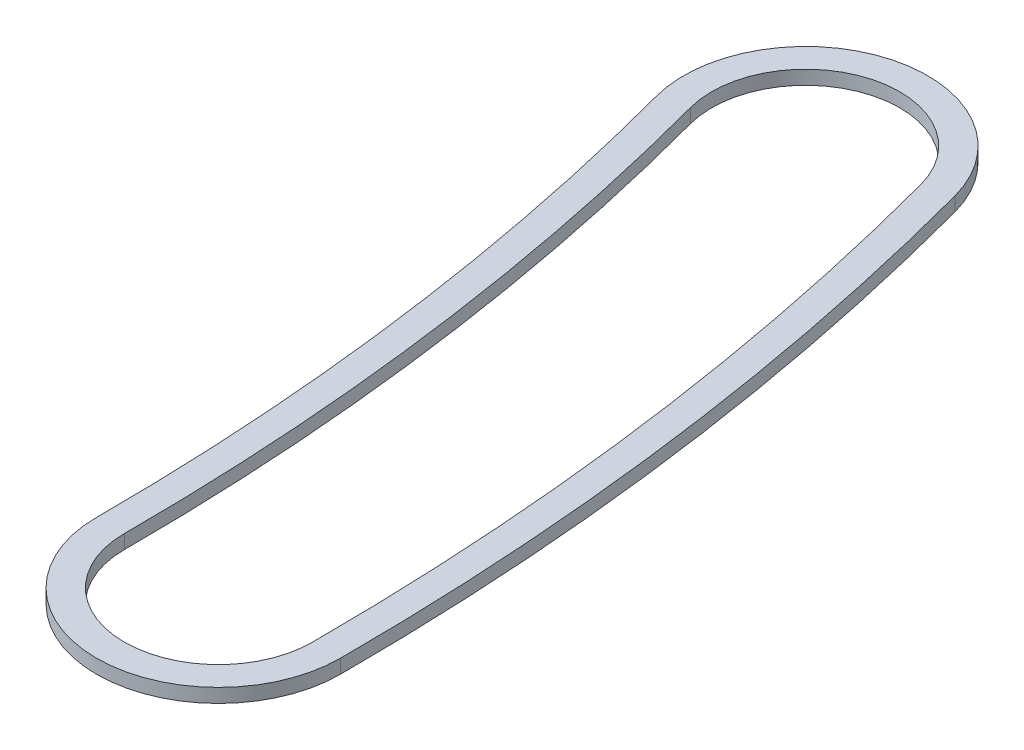
SolidWorks part; units mm, degrees
material "NBR"
ref_plane "Front Plane" through (0, 0, 0) normal (0, 0, 1) x (1, 0, 0)
ref_plane "Top Plane" through (0, 0, 0) normal (0, 1, 0) x (1, 0, 0)
ref_plane "Right Plane" through (0, 0, 0) normal (1, 0, 0) x (0, 0, -1)
sketch "Sketch1" plane through (0, 0, 0) normal (0, 1, 0) x (1, 0, 0)
  line L0 (0, 0) -> (92.0044, 24.6525) construction
  line L1 (0, 0) -> (95.25, 0) construction
  arc A0 (95.25, 0) -> (92.0044, 24.6525) centre (0, 0) ccw construction
  arc A1 (99.695, 0) -> (96.298, 25.803) centre (0, 0) ccw
  arc A2 (90.805, 0) -> (87.7109, 23.5021) centre (0, 0) ccw
  arc A3 (90.805, 0) -> (99.695, 0) centre (95.25, 0) ccw
  arc A4 (96.298, 25.803) -> (87.7109, 23.5021) centre (92.0044, 24.6525) ccw
  arc A5 (95.25, 0) -> (92.0044, 24.6525) centre (0, 0) ccw construction
  arc A6 (98.679, 0) -> (95.3166, 25.54) centre (0, 0) ccw
  arc A7 (91.821, 0) -> (88.6923, 23.765) centre (0, 0) ccw
  arc A8 (91.821, 0) -> (98.679, 0) centre (95.25, 0) ccw
  arc A9 (95.3166, 25.54) -> (88.6923, 23.765) centre (92.0044, 24.6525) ccw
  point P4 (94.4351, 12.4326)
  point P13 (94.4351, 12.4326)
  dimension "D4" = 95.25
  dimension "D3" = 4.445
  dimension "D2" = 1.016
  dimension "D1" = 15
extrude "Boss-Extrude1" add sketch "Sketch1" along normal blind 0.508
equation "\"w\"= 0.04"
equation "\"D2@Sketch1\"=\"w\""
equation "\"D3@Sketch1\"= .185 - .01 '10 thou smaller than channel rad"
